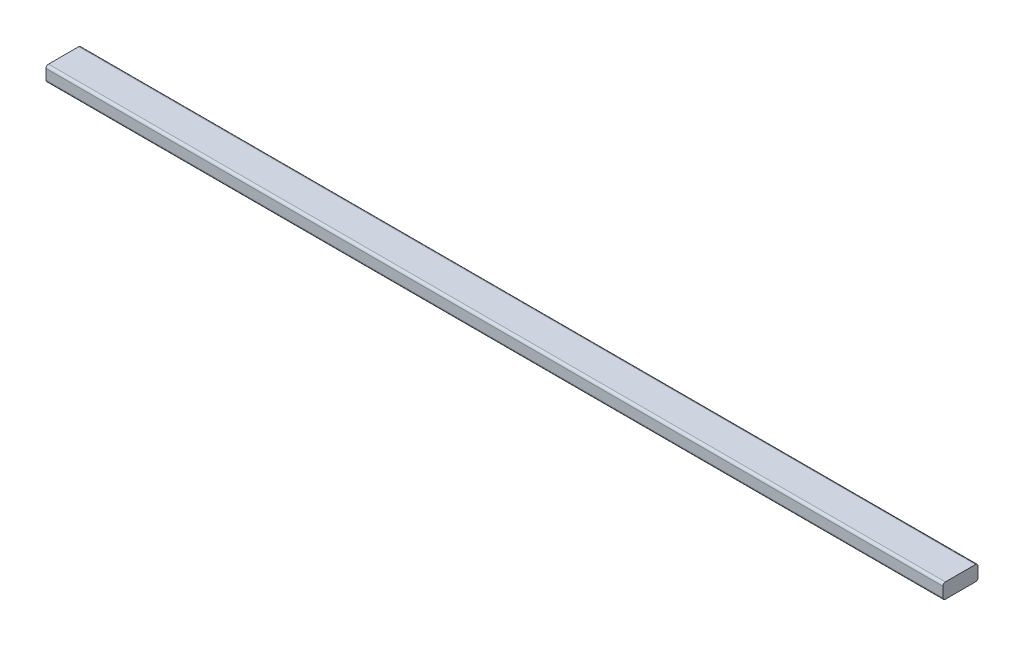
SolidWorks part; units mm, degrees
material "Pine"
ref_plane "Front Plane" through (0, 0, 0) normal (0, 0, 1) x (1, 0, 0)
ref_plane "Top Plane" through (0, 0, 0) normal (0, 1, 0) x (1, 0, 0)
ref_plane "Right Plane" through (0, 0, 0) normal (1, 0, 0) x (0, 0, -1)
sketch "Sketch1" plane through (0, 0, 0) normal (1, 0, 0) x (0, 0, -1)
  line L1 (-38.1, -19.05) -> (38.1, -19.05)
  line L2 (-44.45, -12.7) -> (-44.45, 12.7)
  line L3 (-38.1, 19.05) -> (38.1, 19.05)
  line L4 (44.45, -12.7) -> (44.45, 12.7)
  line L5 (-44.45, -19.05) -> (44.45, 19.05) construction
  line L6 (-44.45, 19.05) -> (44.45, -19.05) construction
  arc A0 (-38.1, -19.05) -> (-44.45, -12.7) centre (-38.1, -12.7) cw
  arc A1 (38.1, -19.05) -> (44.45, -12.7) centre (38.1, -12.7) ccw
  arc A2 (38.1, 19.05) -> (44.45, 12.7) centre (38.1, 12.7) cw
  arc A3 (-44.45, 12.7) -> (-38.1, 19.05) centre (-38.1, 12.7) cw
  point P0 (0, 0)
  dimension "D3" = 6.35
  dimension "D1" = 38.1
  dimension "D2" = 88.9
extrude "Boss-Extrude1" add sketch "Sketch1" along normal mid plane 2268.22
